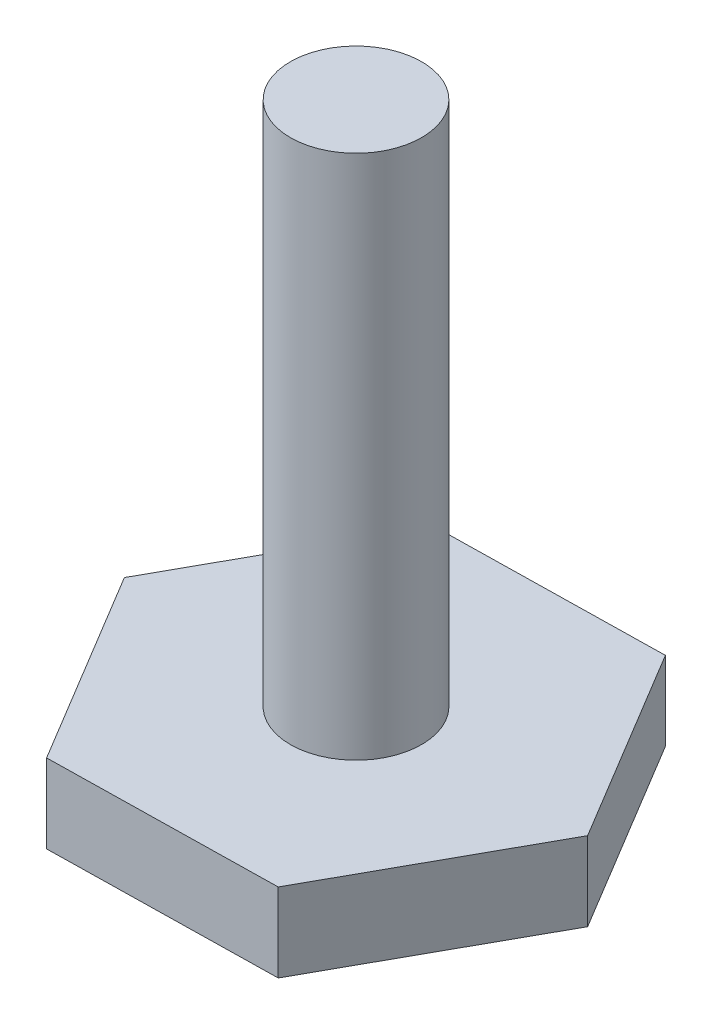
SolidWorks part; units mm, degrees
ref_plane "前视基准面" through (0, 0, 0) normal (0, 0, 1) x (1, 0, 0)
ref_plane "上视基准面" through (0, 0, 0) normal (0, 1, 0) x (1, 0, 0)
ref_plane "右视基准面" through (0, 0, 0) normal (1, 0, 0) x (0, 0, -1)
sketch "草图1" plane through (0, 0, 0) normal (0, 1, 0) x (1, 0, 0)
  line L1 (17.851, -29.6874) -> (34.6355, 0.6157)
  line L2 (34.6355, 0.6157) -> (16.7845, 30.3031)
  line L3 (16.7845, 30.3031) -> (-17.851, 29.6874)
  line L4 (-17.851, 29.6874) -> (-34.6355, -0.6157)
  line L5 (-34.6355, -0.6157) -> (-16.7845, -30.3031)
  line L6 (-16.7845, -30.3031) -> (17.851, -29.6874)
  circle A0 centre (0, 0) radius 30 construction
extrude "凸台-拉伸1" add sketch "草图1" along normal blind 12
sketch "草图2" plane through (0, 12, 0) normal (0, 1, 0) x (1, 0, 0)
  circle A0 centre (0, 0) radius 10
extrude "凸台-拉伸2" add sketch "草图2" along normal blind 80
